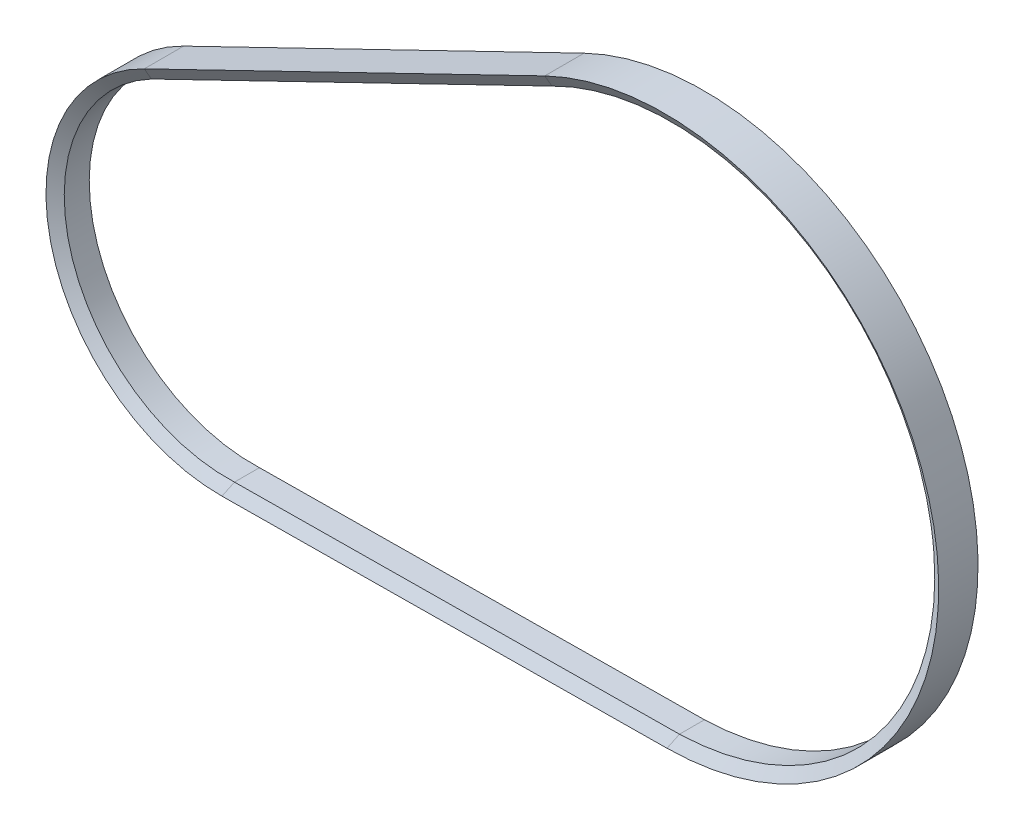
SolidWorks part; units mm, degrees
ref_plane "Front Plane" through (0, 0, 0) normal (0, 0, 1) x (1, 0, 0)
ref_plane "Top Plane" through (0, 0, 0) normal (0, 1, 0) x (1, 0, 0)
ref_plane "Right Plane" through (0, 0, 0) normal (1, 0, 0) x (0, 0, -1)
sketch "Sketch1" plane through (0, 0, 0) normal (0, 0, 1) x (1, 0, 0)
  line L2 (24.0207, -129.9272) -> (-190.8156, -131.9524)
  line L3 (-228.3219, 27.9553) -> (-34.9902, 121.6656)
  arc A0 (-34.9902, 121.6656) -> (24.0207, -129.9272) centre (22.7724, 2.4969) cw
  arc A1 (-190.8156, -131.9524) -> (-228.3219, 27.9553) centre (-191.6091, -47.7861) cw
ref_plane "Plane1" through (-34.9902, 0, 0) normal (1, 0, 0) x (0, 0, -1)
sketch "Sketch2" plane through (-34.9902, 0, 0) normal (1, 0, 0) x (0, 0, -1)
  line L7 (6.04, 115.6656) -> (-6.03, 115.6656)
  line L8 (-6.03, 115.6656) -> (-9.4941, 121.6656)
  line L9 (-9.4941, 121.6656) -> (9.5041, 121.6656)
  line L10 (9.5041, 121.6656) -> (6.04, 115.6656)
  line L11 (0, 126.6216) -> (0, 105.6569) construction
  line L12 (0, 134.9269) -> (0, -129.9272) construction
  dimension "D1" = 6.04
  dimension "D2" = 6
  dimension "D3" = 60
  dimension "D4" = 60
  dimension "D5" = 12.07
sweep "Sweep1" add profiles "Sketch2" path "Sketch1"
